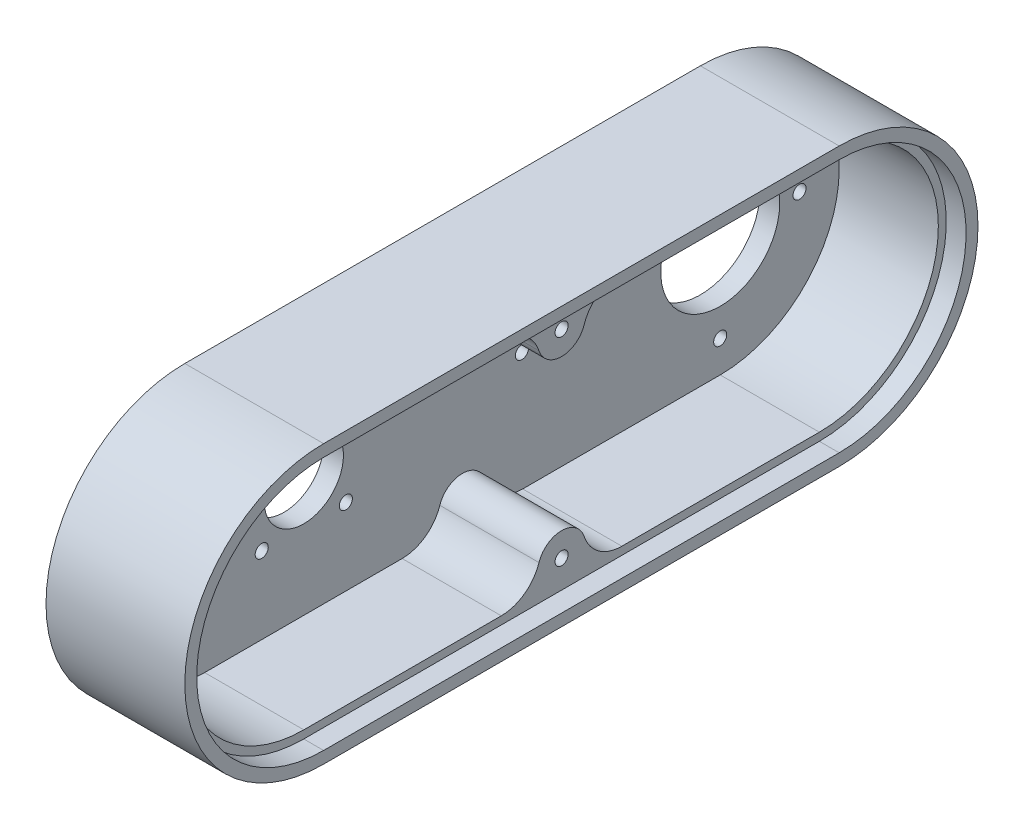
SolidWorks part; units mm, degrees
ref_plane "정면" through (0, 0, 0) normal (0, 0, 1) x (1, 0, 0)
ref_plane "윗면" through (0, 0, 0) normal (0, 1, 0) x (1, 0, 0)
ref_plane "우측면" through (0, 0, 0) normal (1, 0, 0) x (0, 0, -1)
sketch "스케치1" plane through (0, 0, 0) normal (1, 0, 0) x (0, 0, -1)
  line L0 (-1083.263, -22.2895) -> (48916.737, -22.2895) construction
  line L1 (-48.263, 12.7105) -> (81.737, 12.7105)
  line L3 (-48.263, -57.2895) -> (81.737, -57.2895)
  arc A4 (-48.263, 12.7105) -> (-48.263, -57.2895) centre (-48.263, -22.2895) ccw
  arc A5 (81.737, -57.2895) -> (81.737, 12.7105) centre (81.737, -22.2895) ccw
  point P8 (116.737, 12.7105)
  point P11 (-83.263, -57.2895)
  point P14 (-83.263, 12.7105)
  dimension "D3" = 35
  dimension "D4" = 35
  dimension "D1" = 70
  dimension "D2" = 200
  dimension "D5" = 130
extrude "보스-돌출1" add sketch "스케치1" along normal blind 35
sketch "스케치2" plane through (0, 0, 0) normal (-1, 0, 0) x (0, 0, 1)
  line L0 (-1038.5373, 12.7105) -> (48961.4627, 12.7105) construction
  line L1 (-81.737, 12.7105) -> (48.263, 12.7105) construction
  line L2 (-1020.2333, -57.3163) -> (48979.7667, -57.3163) construction
  line L3 (23.263, -22.3029) -> (-35332.076, -35377.6419) construction
  line L4 (-116.737, -1002.7262) -> (-116.737, 48997.2738) construction
  line L5 (23.263, -22.3029) -> (-35332.076, 35333.0362) construction
  line L6 (83.263, -1008.4848) -> (83.263, 48991.5152) construction
  line L8 (-938.505, -22.3029) -> (49061.495, -22.3029) construction
  line L9 (53.263, 12.7105) -> (8.263, 12.7105) construction
  line L10 (53.263, 12.7105) -> (53.263, -57.3163) construction
  line L11 (53.263, -57.3163) -> (8.263, -57.3163) construction
  line L12 (8.263, 12.7105) -> (8.263, -57.3163) construction
  circle A0 centre (53.263, -22.3029) radius 2 construction
  circle A1 centre (23.263, -22.3029) radius 15
  circle A2 centre (33.8696, -11.6963) radius 2 construction
  circle A3 centre (33.8696, -32.9095) radius 2 construction
  circle A4 centre (12.6564, -11.6963) radius 2 construction
  circle A5 centre (12.6564, -32.9095) radius 2 construction
  circle A6 centre (53.263, -7.3029) radius 2 construction
  circle A7 centre (53.263, -37.3029) radius 2 construction
  circle A9 centre (23.263, -22.3029) radius 10
  circle A10 centre (-81.737, -22.3029) radius 15
  arc A11 (-81.737, 12.7105) -> (-81.737, -57.2895) centre (-81.737, -22.2895) ccw construction
  point P16 (53.263, -22.3029)
  dimension "D1" = 15
  dimension "D2" = 30
  dimension "D3" = 4
  dimension "D4" = 45
  dimension "D7" = 35
  dimension "D5" = 15
  dimension "D6" = 15
extrude "컷-돌출1" cut sketch "스케치2" against normal through all both and the other way through all contours A4 | A5 | A2 | A6 | A0 | A7 | A3 | A9 | A10
sketch "스케치3" plane through (35, 0, 0) normal (1, 0, 0) x (0, 0, -1)
  line L13 (81.737, 7.7105) -> (-48.263, 7.7105)
  line L15 (-48.263, -52.2895) -> (81.737, -52.2895)
  line L17 (81.737, 7.7105) -> (-48.263, 7.7105)
  line L19 (-48.263, -52.2895) -> (81.737, -52.2895)
  arc A2 (-48.263, 7.7105) -> (-48.263, -52.2895) centre (-48.263, -22.2895) ccw
  arc A3 (-48.263, 7.7105) -> (-48.263, -52.2895) centre (-48.263, -22.2895) ccw
  arc A4 (81.737, -52.2895) -> (81.737, 7.7105) centre (81.737, -22.2895) ccw
  arc A5 (81.737, -52.2895) -> (81.737, 7.7105) centre (81.737, -22.2895) ccw
  dimension "D1" = 5
extrude "컷-돌출2" cut sketch "스케치3" against normal blind 30
sketch "스케치4" plane through (0, 0, 0) normal (-1, 0, 0) x (0, 0, 1)
  line L0 (-1082.4298, 12.7105) -> (48917.5702, 12.7105) construction
  line L2 (-1069.2501, -57.2895) -> (48930.7499, -57.2895) construction
  line L4 (-116.737, -1000.8602) -> (-116.737, 48999.1398) construction
  line L6 (83.263, -1020.218) -> (83.263, 48979.782) construction
  line L8 (-81.737, 12.7105) -> (48.263, 12.7105) construction
  point P7 (-116.737, -27.2895)
  point P9 (-116.737, -17.2895)
  point P13 (83.263, -27.2895)
sketch "스케치5" plane through (35, 0, 0) normal (1, 0, 0) x (0, 0, -1)
  line L5 (-48.263, -54.2895) -> (81.737, -54.2895)
  line L6 (81.737, 9.7105) -> (-48.263, 9.7105)
  line L7 (-48.263, -52.2895) -> (81.737, -52.2895)
  line L8 (81.737, 7.7105) -> (-48.263, 7.7105)
  line L9 (-48.263, -52.2895) -> (81.737, -52.2895)
  line L12 (81.737, 7.7105) -> (-48.263, 7.7105)
  arc A11 (-48.263, 9.7105) -> (-48.263, -54.2895) centre (-48.263, -22.2895) ccw
  arc A12 (81.737, -54.2895) -> (81.737, 9.7105) centre (81.737, -22.2895) ccw
  arc A13 (81.737, -52.2895) -> (81.737, 7.7105) centre (81.737, -22.2895) ccw
  arc A14 (-48.263, 7.7105) -> (-48.263, -52.2895) centre (-48.263, -22.2895) ccw
  arc A15 (81.737, -52.2895) -> (81.737, 7.7105) centre (81.737, -22.2895) ccw
  arc A18 (-48.263, 7.7105) -> (-48.263, -52.2895) centre (-48.263, -22.2895) ccw
  dimension "D1" = 0
  dimension "D2" = 2
extrude "컷-돌출3" cut sketch "스케치5" against normal blind 5
sketch "스케치8" plane through (0, 0, 0) normal (-1, 0, 0) x (0, 0, 1)
  line L0 (-81.737, -22.3029) -> (49918.263, -22.3029) construction
  line L1 (-81.737, -22.3029) -> (-81.737, 49977.6971) construction
  circle A0 centre (-81.737, -44.3029) radius 2
  circle A1 centre (-81.737, -0.3029) radius 2
  circle A2 centre (-101.737, -22.3029) radius 2
  circle A3 centre (-31.737, -22.3029) radius 2
  dimension "D1" = 4
  dimension "D2" = 4
  dimension "D3" = 4
  dimension "D7" = 4
  dimension "D4" = 22
  dimension "D5" = 20
  dimension "D6" = 22
  dimension "D8" = 50
sketch "스케치10" plane through (5, 0, 0) normal (1, 0, 0) x (0, 0, -1)
  line L0 (16.737, -23.0409) -> (16.737, 49976.9591) construction
  line L2 (-48.263, 12.7105) -> (-48.263, -49987.2895) construction
  line L3 (-23.1252, 12.7105) -> (-50023.1252, 12.7105) construction
  line L5 (-18.3175, -57.2895) -> (-50018.3175, -57.2895) construction
  line L7 (81.737, 12.7105) -> (-48.263, 12.7105) construction
  line L8 (-48.263, -57.2895) -> (81.737, -57.2895) construction
  circle A0 centre (16.737, 2.7105) radius 6
  circle A1 centre (16.737, -47.2895) radius 6
  dimension "D2" = 12
  dimension "D3" = 12
  dimension "D1" = 65
  dimension "D4" = 10
  dimension "D5" = 10
extrude "보스-돌출2" add sketch "스케치10" along normal blind 25
fillet "필렛1" radius 10 4 edges at (17.5, -52.2895, -13.4204) (17.5, -52.2895, -20.0536) (17.5, 7.7105, -20.0536) (17.5, 7.7105, -13.4204)
sketch "스케치11" plane through (30, 0, 0) normal (1, 0, 0) x (0, 0, -1)
  line L0 (16.737, 2.7105) -> (16.737, 50002.7105) construction
  line L1 (28.2507, 12.6971) -> (50028.2507, 12.6971) construction
  line L3 (28.4527, -57.3029) -> (50028.4527, -57.3029) construction
  line L5 (81.737, -22.2895) -> (81.737, 49977.7105) construction
  line L6 (81.737, -22.3029) -> (44.6123, -22.3029) construction
  circle A0 centre (16.737, 2.6971) radius 2
  circle A1 centre (16.737, -47.3029) radius 2
  dimension "D3" = 4
  dimension "D4" = 4
  dimension "D1" = 35
  dimension "D2" = 35
  dimension "D5" = 10
  dimension "D6" = 10
hole_wizard "M4 나사 구멍1" positions "스케치12" profile "스케치13" tap size "M4" standard "ISO"
sketch "스케치12" plane through (30, 0, 0) normal (1, 0, 0) x (0, 0, -1)
  point P0 (16.737, 2.6971)
  point P3 (16.737, -47.3029)
sketch "스케치13" plane through (30, 2.6971, -16.737) normal (0, 1, 0) x (0, 0, -1)
  line L0 (0, 0) -> (0, 12.4914)
  line L1 (0, 12.4914) -> (1.65, 11.5)
  line L2 (1.65, 11.5) -> (1.65, 0)
  line L5 (1.65, 0) -> (0, 0)
  line L10 (0, 12.4914) -> (-1.65, 11.5) construction
  line L11 (0, -6.35) -> (0, 107.95) construction
  dimension "탭 드릴 지름" = 3.3
  dimension "탭 드릴 깊이" = 11.5
  dimension "드릴 각도" = 118
cosmetic thread "구멍 나사산1" parameters "D1"=8, "D2"=4
cosmetic thread "구멍 나사산2" parameters "D1"=8, "D2"=4
hole_wizard "M4 나사 구멍2" positions "스케치14" profile "스케치15" tap size "M4" standard "ISO" end condition through all
sketch "스케치14" plane through (5, 0, 0) normal (1, 0, 0) x (0, 0, -1)
  point P0 (-33.8696, -11.6963)
  point P3 (-12.6564, -11.6963)
  point P6 (-12.6564, -32.9095)
  point P9 (-33.8696, -32.9095)
  point P12 (-53.263, -37.3029)
  point P15 (-53.263, -22.3029)
  point P18 (-53.263, -7.3029)
  point P21 (81.737, -0.3029)
  point P24 (101.737, -22.3029)
  point P27 (81.737, -44.3029)
  point P31 (31.737, -22.3029)
sketch "스케치15" plane through (5, -11.6963, 33.8696) normal (0, 1, 0) x (0, 0, -1)
  line L0 (0, 0) -> (0, 5)
  line L1 (0, 5) -> (1.65, 5)
  line L2 (1.65, 5) -> (1.65, 0)
  line L5 (1.65, 0) -> (0, 0)
  line L11 (0, -6.35) -> (0, 107.95) construction
  dimension "관통 탭 드릴 지름" = 3.3
  dimension "관통 탭 드릴 깊이" = 5
cosmetic thread "구멍 나사산3" parameters "D2"=4
cosmetic thread "구멍 나사산4" parameters "D2"=4
cosmetic thread "구멍 나사산5" parameters "D2"=4
cosmetic thread "구멍 나사산6" parameters "D2"=4
cosmetic thread "구멍 나사산7" parameters "D2"=4
cosmetic thread "구멍 나사산8" parameters "D2"=4
cosmetic thread "구멍 나사산9" parameters "D2"=4
cosmetic thread "구멍 나사산10" parameters "D2"=4
cosmetic thread "구멍 나사산11" parameters "D2"=4
cosmetic thread "구멍 나사산12" parameters "D2"=4
cosmetic thread "구멍 나사산13" parameters "D2"=4
